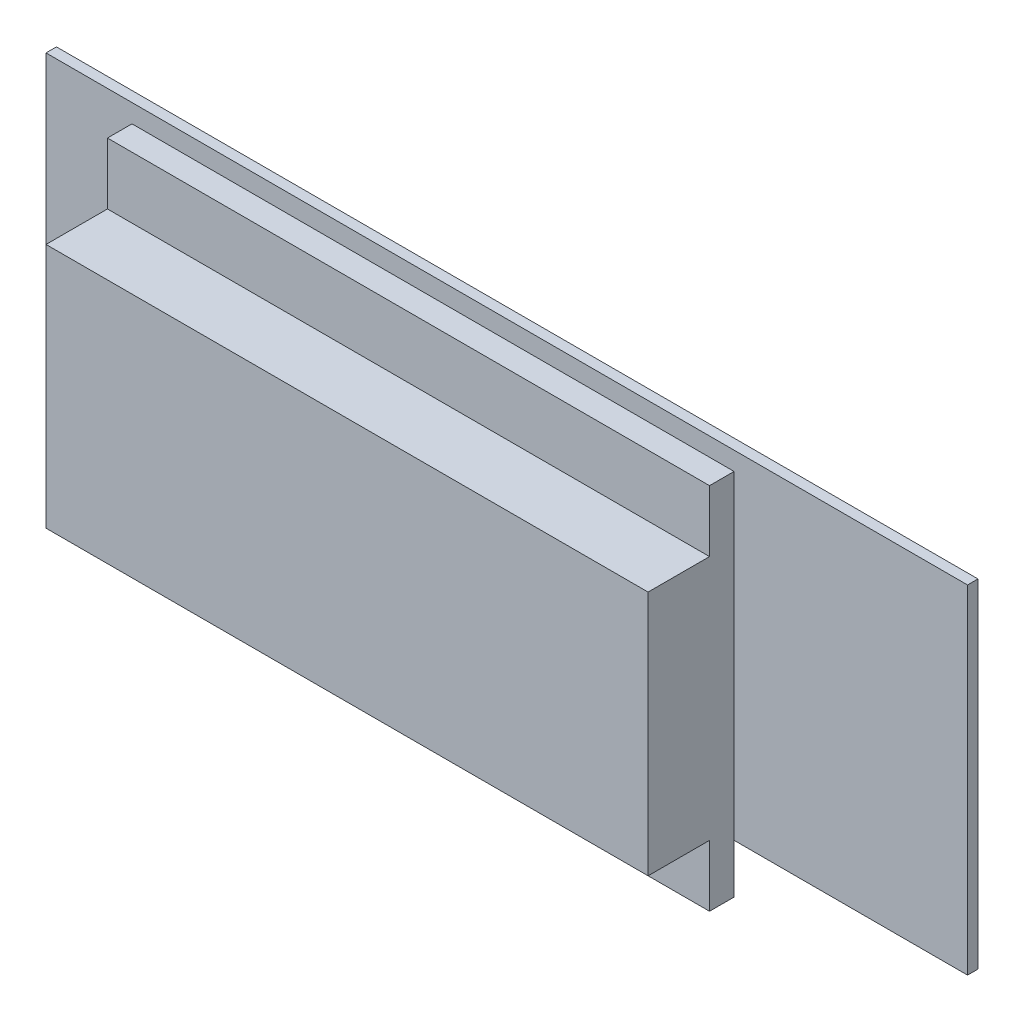
SolidWorks part; units mm, degrees
ref_plane "Piano frontale" through (0, 0, 0) normal (0, 0, 1) x (1, 0, 0)
ref_plane "Piano superiore" through (0, 0, 0) normal (0, 1, 0) x (1, 0, 0)
ref_plane "Piano destro" through (0, 0, 0) normal (1, 0, 0) x (0, 0, -1)
sketch "Schizzo1" plane through (0, 0, 0) normal (0, 0, 1) x (1, 0, 0)
  line L0 (-75, 57.9268) -> (-75, -67.107) construction
  line L1 (75, -27.5) -> (-75, -27.5)
  line L2 (75, -27.5) -> (75, 27.5)
  line L3 (75, 27.5) -> (-75, 27.5)
  line L4 (-75, -27.5) -> (-75, 27.5)
  line L5 (75, -27.5) -> (-75, 27.5) construction
  line L6 (75, 27.5) -> (-75, -27.5) construction
  line L7 (-61, 24.5) -> (-61, -35.5) construction
  line L8 (37, 24.5) -> (37, -35.5) construction
  line L9 (-110.8967, 27.5) -> (115.6497, 27.5) construction
  line L10 (-61, 24.5) -> (37, 24.5) construction
  line L12 (-61, -35.5) -> (37, -35.5) construction
  line L13 (-61, 57.9268) -> (-61, -67.107) construction
  line L14 (-110.8967, 24.5) -> (115.6497, 24.5) construction
  line L15 (37, 57.9268) -> (37, -67.107) construction
  point P0 (0, 0)
  point P16 (-111.3967, -34.5)
  point P17 (115.1497, -34.5)
  dimension "D1" = 150
  dimension "D2" = 55
  dimension "D3" = 14
  dimension "D4" = 98
  dimension "D5" = 3
extrude "Estrusione-Estrusione1" add sketch "Schizzo1" along normal blind 1.7
sketch "Schizzo2" plane through (0, 0, 1.7) normal (0, 0, 1) x (1, 0, 0)
  line L0 (-61, 24.5) -> (-61, -35.5) construction
  line L1 (-61, 24.5) -> (37, 24.5) construction
  line L2 (37, 24.5) -> (37, -35.5) construction
  line L3 (-61, -35.5) -> (37, -35.5) construction
  line L12 (-61, 24.5) -> (-61, -35.5)
  line L13 (-61, 24.5) -> (37, 24.5)
  line L14 (37, 24.5) -> (37, -35.5)
  line L15 (-61, -35.5) -> (37, -35.5)
extrude "Estrusione-Estrusione2" add sketch "Schizzo2" along normal blind 4
sketch "Schizzo3" plane through (0, 0, 5.7) normal (0, 0, 1) x (1, 0, 0)
  line L0 (-61, 24.5) -> (37, 24.5) construction
  line L1 (-61, -35.5) -> (37, -35.5) construction
  line L2 (-61, 14.5) -> (37, 14.5)
  line L3 (-61, -25.5) -> (37, -25.5)
  line L4 (-61, 14.5) -> (-61, -25.5)
  line L5 (37, 14.5) -> (37, -25.5)
  dimension "D1" = 10
  dimension "D2" = 10
extrude "Estrusione-Estrusione3" add sketch "Schizzo3" along normal blind 10
sketch "Schizzo4" plane through (0, 0, 1.7) normal (0, 0, 1) x (1, 0, 0)
  line L0 (19.3715, 27.5) -> (126.3979, 27.5) construction
  line L1 (75, 27.5) -> (-75, 27.5) construction
  line L2 (19.3715, -2.5) -> (126.3979, -2.5) construction
  line L3 (75, 27.5) -> (75, -66.319) construction
  line L4 (62, 27.5) -> (62, -66.319) construction
  line L6 (37, 23.4564) -> (37, 61.9788) construction
  line L7 (37, 24.5) -> (37, -35.5) construction
  line L8 (75, 23.4564) -> (75, 61.9788)
  circle A0 centre (62, -2.5) radius 4
  dimension "D4" = 8
  dimension "D3" = 38
  dimension "D1" = 30
  dimension "D2" = 13
sketch "Schizzo5" plane through (0, 0, 1.7) normal (0, 0, 1) x (1, 0, 0)
  line L0 (62, -2.5) -> (93.3196, -2.5) construction
  line L1 (62, -19.5) -> (93.3196, -19.5) construction
  line L2 (62, -2.5) -> (62, -19.5) construction
  dimension "D1" = 17
